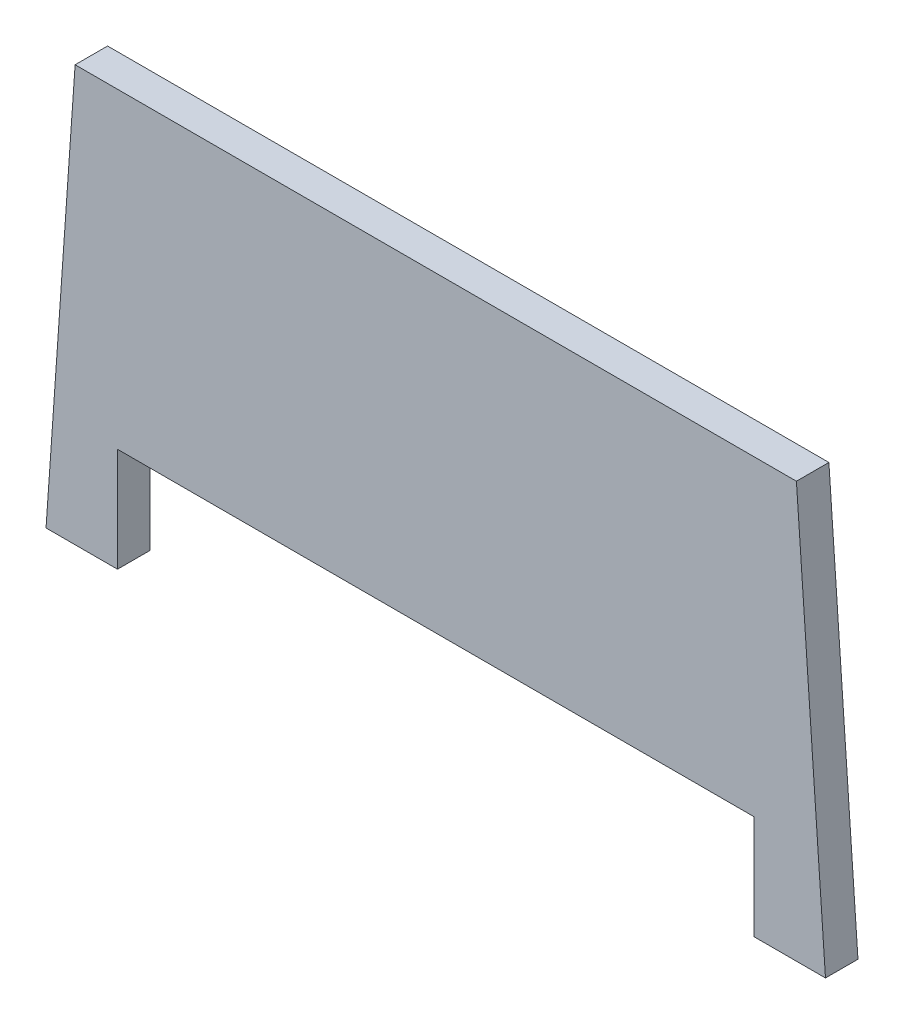
SolidWorks part; units mm, degrees
ref_plane "Front Plane" through (0, 0, 0) normal (0, 0, 1) x (1, 0, 0)
ref_plane "Top Plane" through (0, 0, 0) normal (0, 1, 0) x (1, 0, 0)
ref_plane "Right Plane" through (0, 0, 0) normal (1, 0, 0) x (0, 0, -1)
sketch "Sketch1" plane through (0, 0, 0) normal (0, 0, 1) x (1, 0, 0)
  line L0 (50, 0) -> (185, 0)
  line L1 (185, 0) -> (185, 80)
  line L2 (185, 80) -> (515, 80)
  line L3 (515, 80) -> (515, 0)
  line L4 (515, 0) -> (650, 0)
  line L5 (700, 0) -> (677.6234, 320) construction
  line L6 (627.6234, 320) -> (72.3766, 320)
  line L7 (22.3766, 320) -> (0, 0) construction
  line L8 (0, 0) -> (0, 38.1344) construction
  line L9 (700, 0) -> (700, 152.4204) construction
  line L10 (50, 0) -> (72.3766, 320)
  line L11 (650, 0) -> (627.6234, 320)
  line L12 (22.3766, 320) -> (72.3766, 320) construction
  line L13 (0, 0) -> (50, 0) construction
  line L14 (677.6234, 320) -> (627.6234, 320) construction
  line L15 (650, 0) -> (700, 0)
  point P16 (350, 320)
  point P17 (350, 80)
  dimension "D1" = 4
  dimension "D2" = 4
  dimension "D3" = 700
  dimension "D4" = 80
  dimension "D5" = 320
  dimension "D6" = 330
  dimension "D7" = 50
  dimension "D8" = 50
extrude "Boss-Extrude1" add sketch "Sketch1" along normal blind 25 contours L10 L0 L1 L2 L3 L4 L11 L6
sketch "Sketch3" plane through (0, 0, 25) normal (0, 0, 1) x (1, 0, 0)
  line L0 (50, 0) -> (185, 0) construction
  line L1 (185, 80) -> (105, 80)
  line L2 (185, 80) -> (185, 0)
  line L3 (185, 0) -> (105, 0)
  line L4 (105, 80) -> (105, 0)
  line L5 (515, 0) -> (650, 0) construction
  line L6 (515, 80) -> (595, 80)
  line L7 (515, 80) -> (515, 0)
  line L8 (515, 0) -> (595, 0)
  line L9 (595, 80) -> (595, 0)
  dimension "D1" = 80
  dimension "D2" = 80
extrude "Cut-Extrude2" cut sketch "Sketch3" against normal through all
sketch "Sketch2" plane through (0, 0, 25) normal (0, 0, 1) x (1, 0, 0)
  line L0 (50, 0) -> (105, 0) construction
  line L1 (595, 0) -> (650, 0) construction
  circle A0 centre (145, 33) radius 20
  circle A1 centre (555, 33) radius 20
  dimension "D1" = 145
  dimension "D2" = 40
  dimension "D4" = 410
  dimension "D6" = 40
  dimension "D3" = 33
  dimension "D5" = 33
